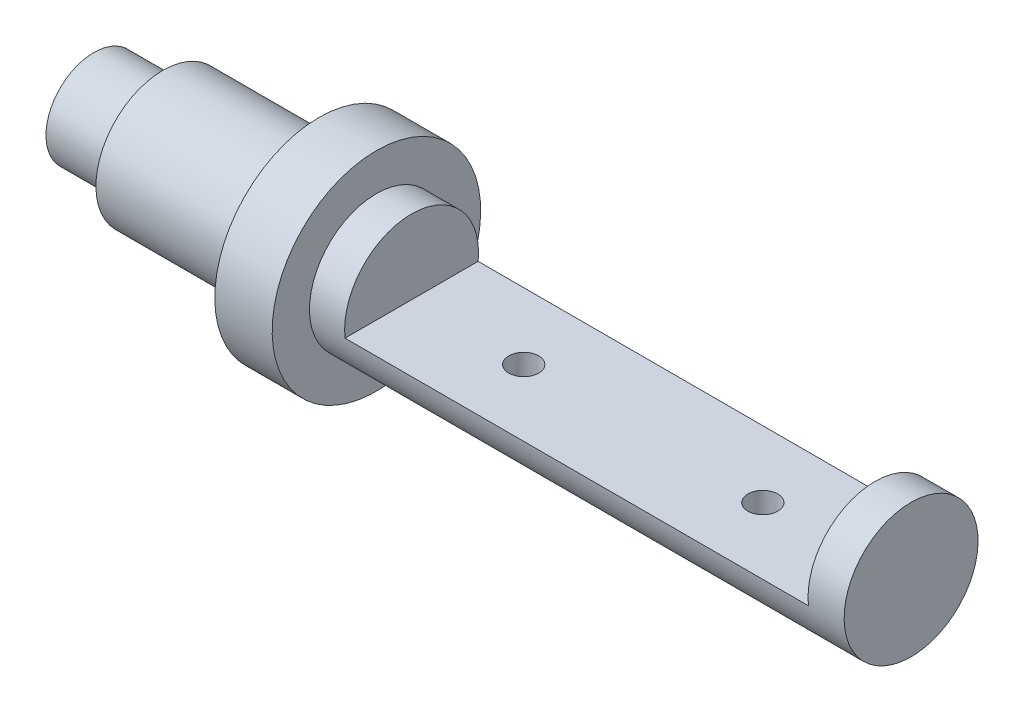
SolidWorks part; units mm, degrees
ref_plane "Front Plane" through (0, 0, 0) normal (0, 0, 1) x (1, 0, 0)
ref_plane "Top Plane" through (0, 0, 0) normal (0, 1, 0) x (1, 0, 0)
ref_plane "Right Plane" through (0, 0, 0) normal (1, 0, 0) x (0, 0, -1)
sketch "Sketch1" plane through (0, 0, 0) normal (0, 0, 1) x (1, 0, 0)
  line L0 (0, 0) -> (0, 20)
  line L1 (0, 20) -> (28.9, 20)
  line L2 (28.9, 20) -> (28.9, 28)
  line L3 (28.9, 28) -> (118.2, 28)
  line L4 (118.2, 28) -> (118.2, 43.6)
  line L5 (118.2, 43.6) -> (94.2, 43.6)
  line L6 (94.2, 43.6) -> (94.2, 28)
  line L7 (94.2, 28) -> (341.8, 28)
  line L8 (341.8, 28) -> (341.8, 0)
  line L9 (341.8, 0) -> (0, 0)
  dimension "D1" = 20
  dimension "D2" = 28
  dimension "D3" = 43.6
  dimension "D4" = 247.6
  dimension "D5" = 28.9
  dimension "D6" = 89.3
  dimension "D7" = 24
revolve "Revolve2" add sketch "Sketch1" angle 360 about L9
sketch "Sketch2" plane through (0, 0, 0) normal (0, 0, 1) x (1, 0, 0)
  line L0 (341.8, 28) -> (118.2, 28) construction
  line L1 (132.9, 28) -> (326.7, 28)
  line L2 (132.9, 28) -> (132.9, -3.1)
  line L3 (132.9, -3.1) -> (326.7, -3.1)
  line L4 (326.7, 28) -> (326.7, -3.1)
  line L5 (341.8, -28) -> (341.8, 28) construction
  dimension "D1" = 15.1
  dimension "D2" = 31.1
  dimension "D3" = 193.8
extrude "Cut-Extrude1" cut sketch "Sketch2" against normal through all both and the other way through all
hole_wizard "Hole1" positions "Sketch3" profile "Sketch4" legacy end condition up to next
sketch "Sketch3" plane through (0, -3.1, 0) normal (0, 1, 0) x (1, 0, 0)
  line L0 (132.9, -28) -> (132.9, 28) construction
  point P0 (179.8, 0)
  point P2 (279.8, 0)
  dimension "D1" = 100
  dimension "D2" = 46.9
sketch "Sketch4" plane through (179.8, -3.1, 0) normal (1, 0, 0) x (0, 0, 1)
  line L0 (0, 0) -> (0, 24.9)
  line L1 (0, 24.9) -> (6.25, 24.9)
  line L2 (6.25, 24.9) -> (6.25, 0)
  line L3 (6.25, 0) -> (0, 0)
  line L4 (0, 110) -> (0, -10) construction
  dimension "Diameter" = 12.5
  dimension "Depth" = 24.9
